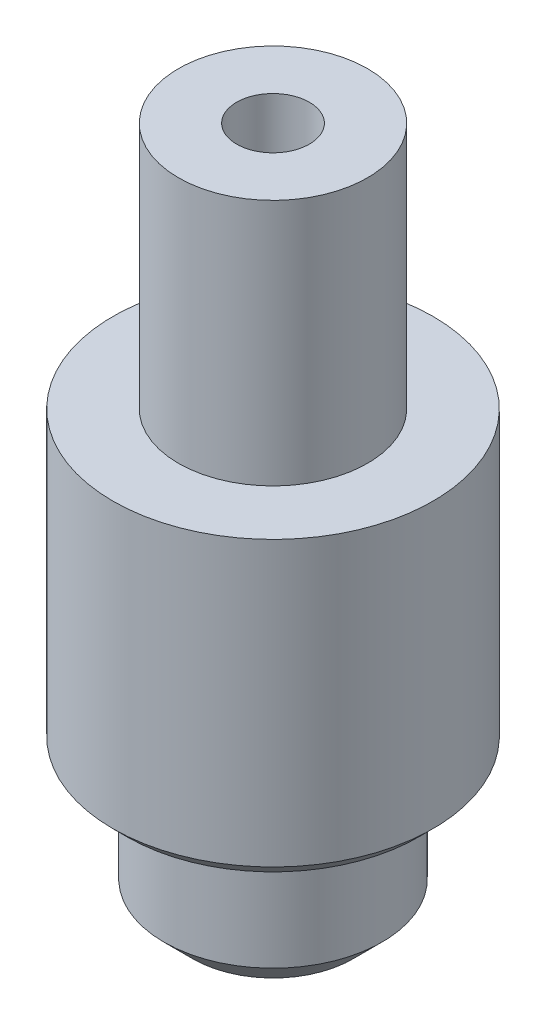
SolidWorks part; units mm, degrees
ref_plane "Front Plane" through (0, 0, 0) normal (0, 0, 1) x (1, 0, 0)
ref_plane "Top Plane" through (0, 0, 0) normal (0, 1, 0) x (1, 0, 0)
ref_plane "Right Plane" through (0, 0, 0) normal (1, 0, 0) x (0, 0, -1)
sketch "Sketch1" plane through (0, 0, 0) normal (0, 0, 1) x (1, 0, 0)
  line L0 (0, -30) -> (0, 17) construction
  line L1 (-7.5, -20.5) -> (-7.5, -30)
  line L2 (-11, 0) -> (-11, -20.5)
  line L3 (-11, -20.5) -> (-7.5, -20.5)
  line L4 (-11, 0) -> (-6.5, 0)
  line L5 (-6.5, 17) -> (-2.5, 17)
  line L6 (-7.5, -30) -> (-2, -30)
  line L7 (-6.5, 17) -> (-6.5, 0)
  line L8 (-2.5, 17) -> (-2.5, -20.5)
  line L9 (-2, -20.5) -> (-2, -30)
  line L10 (-2.5, -20.5) -> (-2, -20.5)
  point P0 (0, 0.001)
  point P1 (0.001, 0.001)
  point P2 (0.001, 0)
  dimension "D1" = 6.5
  dimension "D2" = 11
  dimension "D3" = 2.5
  dimension "D4" = 2
revolve "Revolve1" add sketch "Sketch1" angle 360 about L0
chamfer "Chamfer1" distance 2 angle 45 1 edges at (0, -30, -7.5)
chamfer "Chamfer2" distance 1 angle 45 1 edges at (0, -20.5, -11)
